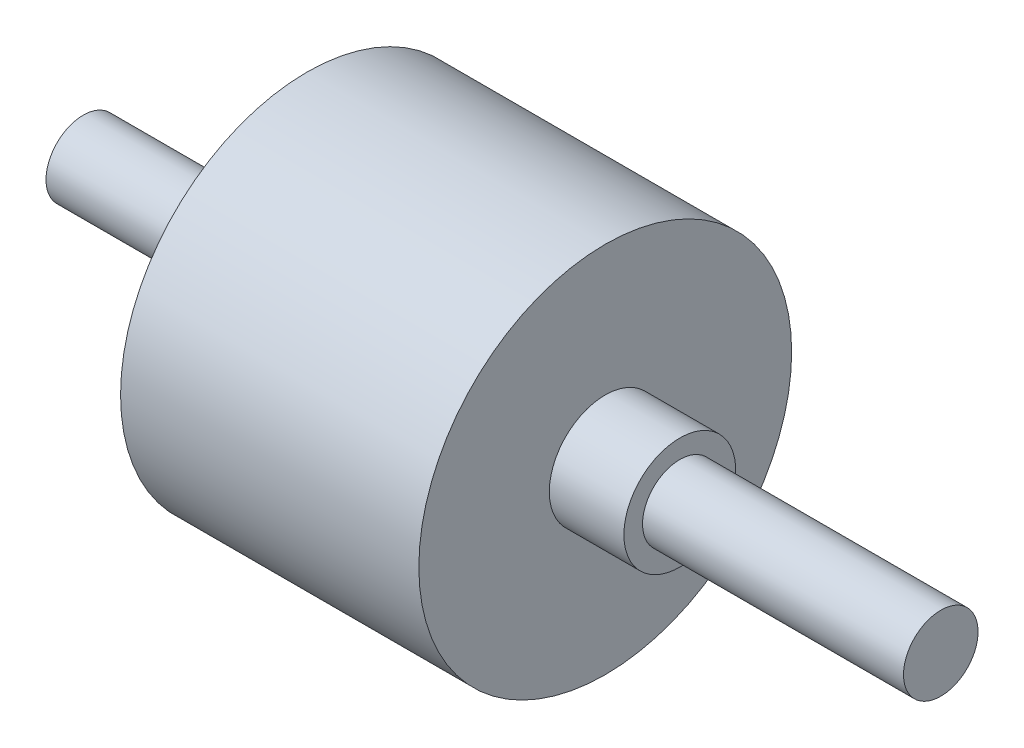
SolidWorks part; units mm, degrees
ref_plane "Front Plane" through (0, 0, 0) normal (0, 0, 1) x (1, 0, 0)
ref_plane "Top Plane" through (0, 0, 0) normal (0, 1, 0) x (1, 0, 0)
ref_plane "Right Plane" through (0, 0, 0) normal (1, 0, 0) x (0, 0, -1)
sketch "Sketch1" plane through (0, 0, 0) normal (0, 1, 0) x (1, 0, 0)
  line L0 (0, 0) -> (113.7362, 0) construction
  line L1 (0, 0) -> (0, 5)
  line L2 (0, 5) -> (30, 5)
  line L3 (30, 5) -> (30, 25)
  line L4 (30, 25) -> (70, 25)
  line L5 (70, 25) -> (70, 7.5)
  line L6 (70, 7.5) -> (80, 7.5)
  line L7 (80, 7.5) -> (80, 5)
  line L8 (80, 5) -> (115, 5)
  line L9 (115, 5) -> (115, 0)
  line L10 (0, 0) -> (115, 0)
  point P7 (113.7362, 0)
  dimension "D1" = 5
  dimension "D2" = 7.5
  dimension "D3" = 25
  dimension "D4" = 30
  dimension "D5" = 40
  dimension "D6" = 10
  dimension "D7" = 115
revolve "Revolve1" add sketch "Sketch1" angle 360 about L0
